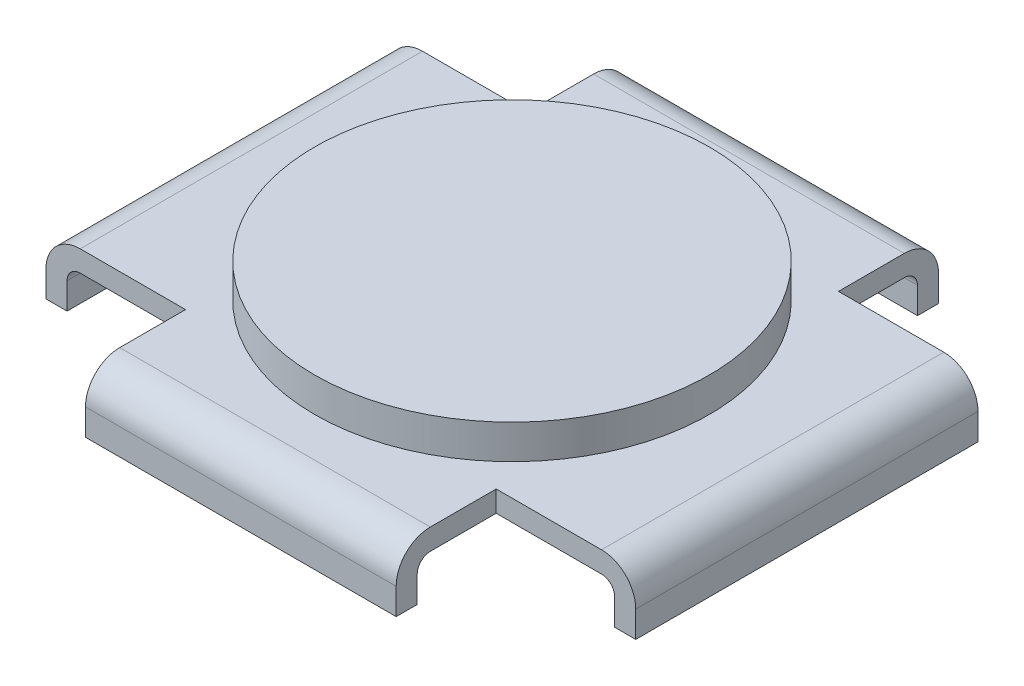
SolidWorks part; units mm, degrees
ref_plane "正面" through (0, 0, 0) normal (0, 0, 1) x (1, 0, 0)
ref_plane "平面" through (0, 0, 0) normal (0, 1, 0) x (1, 0, 0)
ref_plane "右側面" through (0, 0, 0) normal (1, 0, 0) x (0, 0, -1)
sketch "ｽｹｯﾁ1" plane through (0, 0, 0) normal (0, 1, 0) x (1, 0, 0)
  line L1 (-22.4, 20.6) -> (22.4, 20.6)
  line L2 (-22.4, 20.6) -> (-22.4, -20.6)
  line L3 (-22.4, -20.6) -> (22.4, -20.6)
  line L4 (22.4, 20.6) -> (22.4, -20.6)
  line L5 (-22.4, 20.6) -> (22.4, -20.6) construction
  line L6 (-22.4, -20.6) -> (22.4, 20.6) construction
  point P0 (0, 0)
  dimension "D1" = 44.8
  dimension "D2" = 41.2
extrude "ﾎﾞｽ - 押し出し1" add sketch "ｽｹｯﾁ1" along normal blind 4.6
sketch "ｽｹｯﾁ3" plane through (0, 0, 0) normal (0, -1, 0) x (-1, 0, 0)
  line L1 (20.8, -19) -> (-20.8, -19)
  line L2 (20.8, -19) -> (20.8, 19)
  line L3 (20.8, 19) -> (-20.8, 19)
  line L4 (-20.8, -19) -> (-20.8, 19)
  line L5 (20.8, -19) -> (-20.8, 19) construction
  line L6 (20.8, 19) -> (-20.8, -19) construction
  point P0 (0, 0)
  dimension "D1" = 38
  dimension "D2" = 41.6
extrude "ｶｯﾄ - 押し出し1" cut sketch "ｽｹｯﾁ3" against normal blind 3
sketch "ｽｹｯﾁ4" plane through (0, 4.6, 0) normal (0, 1, 0) x (1, 0, 0)
  line L1 (22.4, -20.6) -> (11.8, -20.6)
  line L2 (22.4, -20.6) -> (22.4, -13)
  line L3 (22.4, -13) -> (11.8, -13)
  line L4 (11.8, -20.6) -> (11.8, -13)
  line L5 (22.4, 20.6) -> (11.8, 20.6)
  line L6 (22.4, 20.6) -> (22.4, 13)
  line L7 (22.4, 13) -> (11.8, 13)
  line L8 (11.8, 20.6) -> (11.8, 13)
  line L9 (-22.4, -20.6) -> (-11.8, -20.6)
  line L10 (-22.4, -20.6) -> (-22.4, -13)
  line L11 (-22.4, -13) -> (-11.8, -13)
  line L12 (-11.8, -20.6) -> (-11.8, -13)
  line L13 (-22.4, 20.6) -> (-11.8, 20.6)
  line L14 (-22.4, 20.6) -> (-22.4, 13)
  line L15 (-22.4, 13) -> (-11.8, 13)
  line L16 (-11.8, 20.6) -> (-11.8, 13)
  dimension "D1" = 10.6
  dimension "D2" = 7.6
  dimension "D3" = 7.6
  dimension "D4" = 10.6
  dimension "D5" = 10.6
  dimension "D6" = 7.6
  dimension "D7" = 10.6
  dimension "D8" = 7.6
extrude "ｶｯﾄ - 押し出し2" cut sketch "ｽｹｯﾁ4" against normal through all
fillet "ﾌｨﾚｯﾄ1" radius 2.6 4 edges at (0, 4.6, 20.6) (-22.4, 4.6, 0) (0, 4.6, -20.6) (22.4, 4.6, 0)
fillet "ﾌｨﾚｯﾄ2" radius 1 4 edges at (-20.8, 3, 0) (0, 3, -19) (20.8, 3, 0) (0, 3, 19)
sketch "ｽｹｯﾁ5" plane through (0, 4.6, 0) normal (0, 1, 0) x (1, 0, 0)
  circle A0 centre (0, 0) radius 15
  dimension "D1" = 30
extrude "ﾎﾞｽ - 押し出し2" add sketch "ｽｹｯﾁ5" along normal blind 2.6
